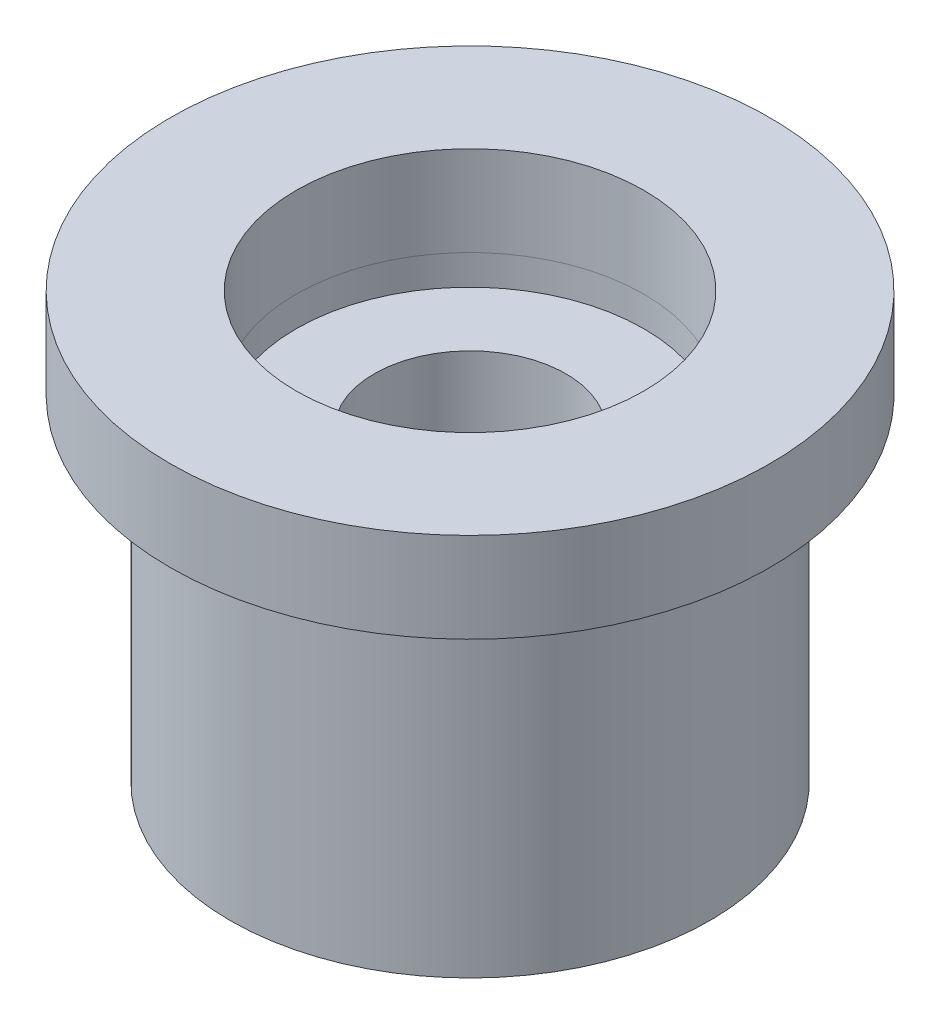
SolidWorks part; units mm, degrees
material "201.0-T7 Moldeo aislado (SS)"
ref_plane "Alzado" through (0, 0, 0) normal (0, 0, 1) x (1, 0, 0)
ref_plane "Planta" through (0, 0, 0) normal (0, 1, 0) x (1, 0, 0)
ref_plane "Vista lateral" through (0, 0, 0) normal (1, 0, 0) x (0, 0, -1)
sketch "Croquis2" plane through (0, 0, 0) normal (0, 1, 0) x (1, 0, 0)
  circle A0 centre (0, 0) radius 4
  dimension "D1" = 8
extrude "Saliente-Extruir2" add sketch "Croquis2" along normal blind 5.6
sketch "Croquis3" plane through (0, 5.6, 0) normal (0, 1, 0) x (1, 0, 0)
  circle A0 centre (0, 0) radius 5
  dimension "D1" = 10
extrude "Saliente-Extruir3" add sketch "Croquis3" along normal blind 1.5 separate body
sketch "Croquis4" plane through (0, 7.1, 0) normal (0, 1, 0) x (1, 0, 0)
  circle A0 centre (0, 0) radius 2.9
  dimension "D1" = 5.8
extrude "Cortar-Extruir2" cut sketch "Croquis4" against normal blind 2
sketch "Croquis6" plane through (0, 5.1, 0) normal (0, 1, 0) x (1, 0, 0)
  circle A0 centre (0, 0) radius 1.6
  dimension "D1" = 3.2
extrude "Cortar-Extruir3" cut sketch "Croquis6" against normal through all
sketch "Croquis7" plane through (0, 0, 0) normal (0, -1, 0) x (1, 0, 0)
  line L0 (2.265, 0.4) -> (3.0741, 0.4)
  line L1 (2.265, -0.4) -> (3.0741, -0.4)
  line L2 (-1.4789, -1.7615) -> (-1.8835, -2.4622)
  line L3 (-0.7861, -2.1615) -> (-1.1906, -2.8622)
  line L4 (-0.7861, 2.1615) -> (-1.1906, 2.8622)
  line L5 (-1.4789, 1.7615) -> (-1.8835, 2.4622)
  arc A0 (-1.4789, 1.7615) -> (-1.4789, -1.7615) centre (0, 0) ccw
  arc A1 (-1.8835, 2.4622) -> (-1.8835, -2.4622) centre (0, 0) ccw
  arc A2 (-0.7861, -2.1615) -> (2.265, -0.4) centre (0, 0) ccw
  arc A3 (-1.1906, -2.8622) -> (3.0741, -0.4) centre (0, 0) ccw
  arc A4 (2.265, 0.4) -> (-0.7861, 2.1615) centre (0, 0) ccw
  arc A5 (3.0741, 0.4) -> (-1.1906, 2.8622) centre (0, 0) ccw
  point P18 (0, 0)
  dimension "D1" = 6.2
  dimension "D2" = 4.6
  dimension "D3" = 0.8
  dimension "D4" = 3
extrude "Cortar-Extruir4" cut sketch "Croquis7" against normal blind 4.3
